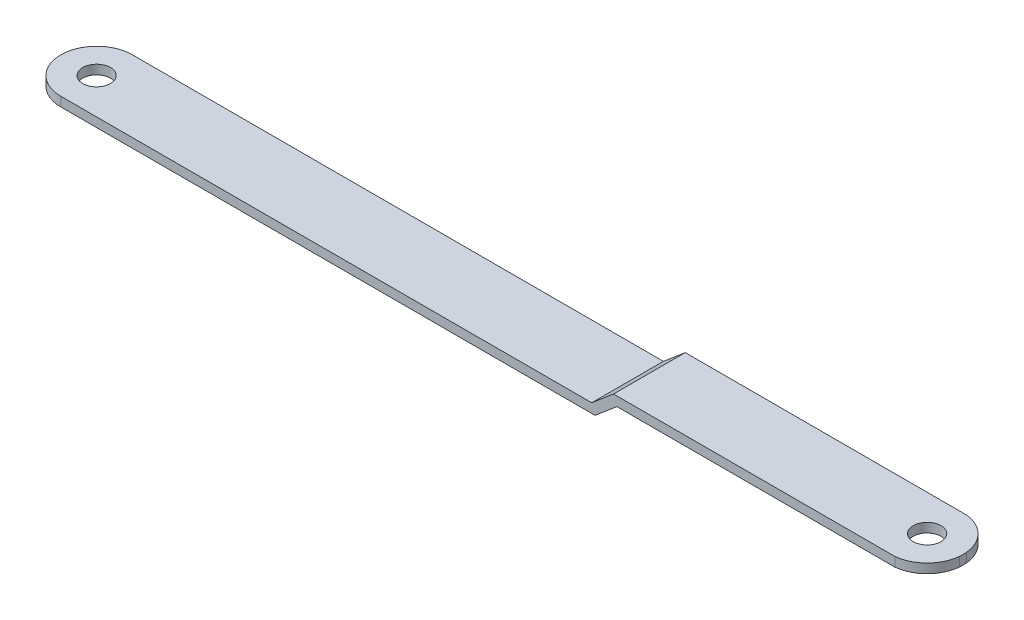
SolidWorks part; units mm, degrees
ref_plane "Спереди" through (0, 0, 0) normal (0, 0, 1) x (1, 0, 0)
ref_plane "Сверху" through (0, 0, 0) normal (0, 1, 0) x (1, 0, 0)
ref_plane "Справа" through (0, 0, 0) normal (1, 0, 0) x (0, 0, -1)
sketch "Эскиз1" plane through (0, 0, 0) normal (0, 0, 1) x (1, 0, 0)
  line L0 (0, 0) -> (122.5, 0)
  line L1 (122.5, 0) -> (127.2194, 4)
  line L2 (127.2194, 4) -> (195, 4)
  point P4 (0, 0)
  point P6 (0, 0)
extrude "Вытянуть-Тонкостенный1" add sketch "Эскиз1" along normal blind 15.5 thin
sketch "Эскиз2" plane through (0, 4, 0) normal (0, 1, 0) x (1, 0, 0)
  line L0 (127.2194, 0) -> (195, 0) construction
  line L1 (127.2194, -15.5) -> (195, -15.5) construction
  line L2 (188.0226, 0) -> (7.75, 0)
  line L4 (7.75, -15.5) -> (188.0226, -15.5)
  line L5 (0, 0) -> (122.5, 0) construction
  line L6 (0, -15.5) -> (122.5, -15.5) construction
  circle A0 centre (187.25, -7.75) radius 3
  arc A1 (188.0226, 0) -> (188.0226, -15.5) centre (187.25, -7.75) cw
  arc A2 (7.75, 0) -> (7.75, -15.5) centre (7.75, -7.75) ccw
  circle A3 centre (7.75, -7.75) radius 3
  point P10 (0, 0)
extrude "Вырез-Вытянуть4" cut sketch "Эскиз2" against normal blind 10 flip side to cut
